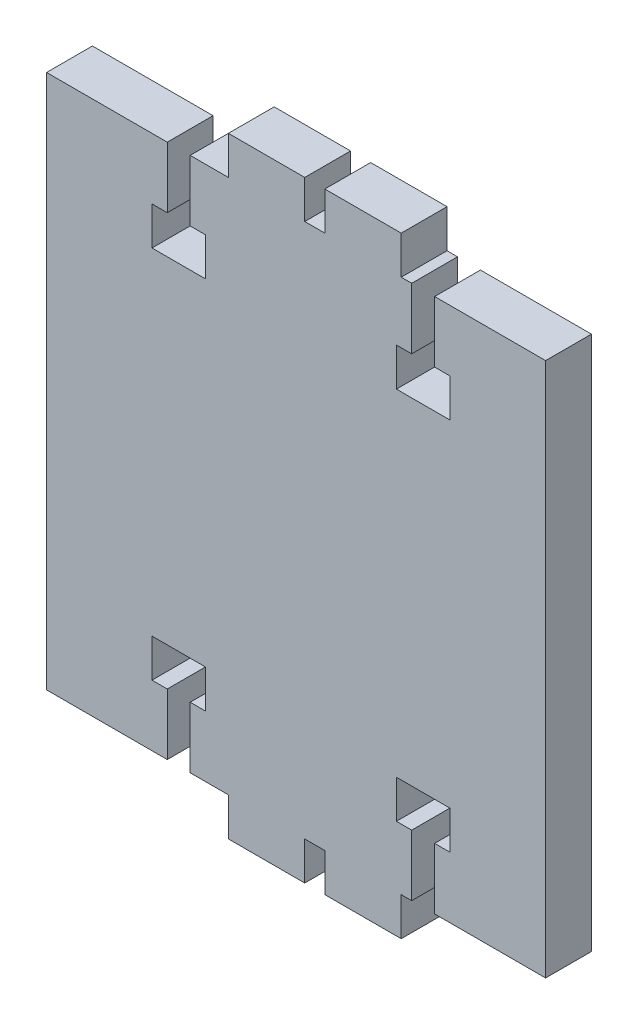
SolidWorks part; units mm, degrees
material "Cedro"
ref_plane "Plano frontal" through (0, 0, 0) normal (0, 0, 1) x (1, 0, 0)
ref_plane "Plano superior" through (0, 0, 0) normal (0, 1, 0) x (1, 0, 0)
ref_plane "Plano direito" through (0, 0, 0) normal (1, 0, 0) x (0, 0, -1)
sketch "Model" plane through (0, 0, 0) normal (0, 0, 1) x (1, 0, 0)
  line L0 (-49.531, 62) -> (-49.531, 70)
  line L1 (-49.531, 70) -> (-65.331, 70)
  line L2 (-65.331, 70) -> (-65.331, 0)
  line L3 (-65.331, 0) -> (-49.531, 0)
  line L4 (-49.531, 0) -> (-49.531, 8)
  line L5 (-49.531, 8) -> (-51.531, 8)
  line L6 (-51.531, 8) -> (-51.531, 13)
  line L7 (-51.531, 13) -> (-44.531, 13)
  line L8 (-44.531, 13) -> (-44.531, 8)
  line L9 (-44.531, 8) -> (-46.531, 8)
  line L10 (-46.531, 8) -> (-46.531, 0)
  line L11 (-46.531, 0) -> (-41.5322, 0)
  line L12 (-41.5322, 0) -> (-41.5322, -5)
  line L13 (-41.5322, -5) -> (-31.5322, -5)
  line L14 (-31.5322, -5) -> (-31.5322, 0)
  line L15 (-31.5322, 0) -> (-28.9043, 0)
  line L16 (-28.9043, 0) -> (-28.9043, -5)
  line L17 (-28.9043, -5) -> (-18.9043, -5)
  line L18 (-18.9043, -5) -> (-18.9043, 0)
  line L19 (-18.9043, 0) -> (-17.531, 0)
  line L20 (-17.531, 0) -> (-17.531, 8)
  line L21 (-17.531, 8) -> (-19.531, 8)
  line L22 (-19.531, 8) -> (-19.531, 13)
  line L23 (-19.531, 13) -> (-12.531, 13)
  line L24 (-12.531, 13) -> (-12.531, 8)
  line L25 (-12.531, 8) -> (-14.531, 8)
  line L26 (-14.531, 8) -> (-14.531, 0)
  line L27 (-14.531, 0) -> (0, 0)
  line L28 (0, 0) -> (0, 70)
  line L29 (0, 70) -> (-14.531, 70)
  line L30 (-14.531, 70) -> (-14.531, 62)
  line L31 (-14.531, 62) -> (-12.531, 62)
  line L32 (-12.531, 62) -> (-12.531, 57)
  line L33 (-12.531, 57) -> (-19.531, 57)
  line L34 (-19.531, 57) -> (-19.531, 62)
  line L35 (-19.531, 62) -> (-17.531, 62)
  line L36 (-17.531, 62) -> (-17.531, 70)
  line L37 (-17.531, 70) -> (-18.904, 70)
  line L38 (-18.904, 70) -> (-18.904, 75)
  line L39 (-18.904, 75) -> (-28.904, 75)
  line L40 (-28.904, 75) -> (-28.904, 70)
  line L41 (-28.904, 70) -> (-31.532, 70)
  line L42 (-31.532, 70) -> (-31.532, 75)
  line L43 (-31.532, 75) -> (-41.532, 75)
  line L44 (-41.532, 75) -> (-41.532, 70)
  line L45 (-41.532, 70) -> (-46.531, 70)
  line L46 (-46.531, 70) -> (-46.531, 62)
  line L47 (-46.531, 62) -> (-44.531, 62)
  line L48 (-44.531, 62) -> (-44.531, 57)
  line L49 (-44.531, 57) -> (-51.531, 57)
  line L50 (-51.531, 57) -> (-51.531, 62)
  line L51 (-51.531, 62) -> (-49.531, 62)
extrude "Ressalto-extrusão1" add sketch "Model" along normal blind 6
